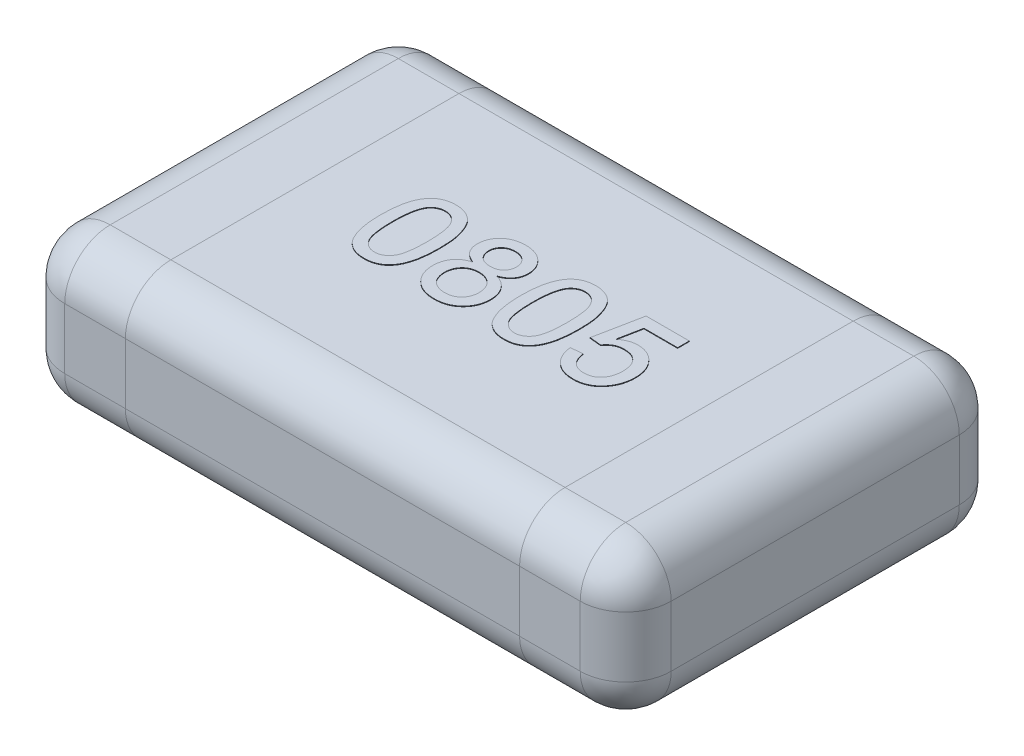
SolidWorks part; units mm, degrees
ref_plane "Front" through (0, 0, 0) normal (0, 0, 1) x (1, 0, 0)
ref_plane "Top" through (0, 0, 0) normal (0, 1, 0) x (1, 0, 0)
ref_plane "Right" through (0, 0, 0) normal (1, 0, 0) x (0, 0, -1)
sketch "Sketch1" plane through (0, 0, 0) normal (0, 1, 0) x (1, 0, 0)
  line L0 (0, -5.3126) -> (0, 5.729) construction
  line L1 (-6.1479, 0) -> (7.7291, 0) construction
  line L3 (-1, 0.625) -> (1, 0.625)
  line L4 (-1, 0.625) -> (-1, -0.625)
  line L5 (-1, -0.625) -> (1, -0.625)
  line L6 (1, 0.625) -> (1, -0.625)
  dimension "D1" = 2
  dimension "D2" = 1.25
extrude "Extrude1" add sketch "Sketch1" along normal blind 0.5
fillet "Fillet1" radius 0.15 12 edges at (0, 0.5, 0.625) (-1, 0.25, -0.625) (0, 0, -0.625) (-1, 0, 0) (-1, 0.25, 0.625) (0, 0, 0.625) (1, 0.25, 0.625) (1, 0.25, -0.625) (1, 0, 0) (0, 0.5, -0.625) (1, 0.5, 0) (-1, 0.5, 0)
sketch "Sketch2" plane through (0, 0, 0.625) normal (0, 0, 1) x (1, 0, 0)
  line L0 (-0.85, 0.5) -> (0.85, 0.5) construction
  line L1 (-0.65, 0.5) -> (0.65, 0.5)
  line L2 (-0.65, 0.5) -> (-0.65, 0)
  line L3 (-0.65, 0) -> (0.65, 0)
  line L4 (0.65, 0.5) -> (0.65, 0)
  line L5 (0.85, 0) -> (-0.85, 0) construction
  line L6 (-1, 0.15) -> (-1, 0.35) construction
  line L7 (0, -0.2963) -> (0, 3.0124) construction
  dimension "D1" = 0.35
split line "Split Line1"
sketch "Sketch3" plane through (0, 0.5, 0) normal (0, 1, 0) x (1, 0, 0)
  text T0 "0805" font "Arial" height 0.3
  dimension "D1" = 0.45
  dimension "D2" = 0.15
extrude "Extrude2" add sketch "Sketch3" along normal blind 0.002
